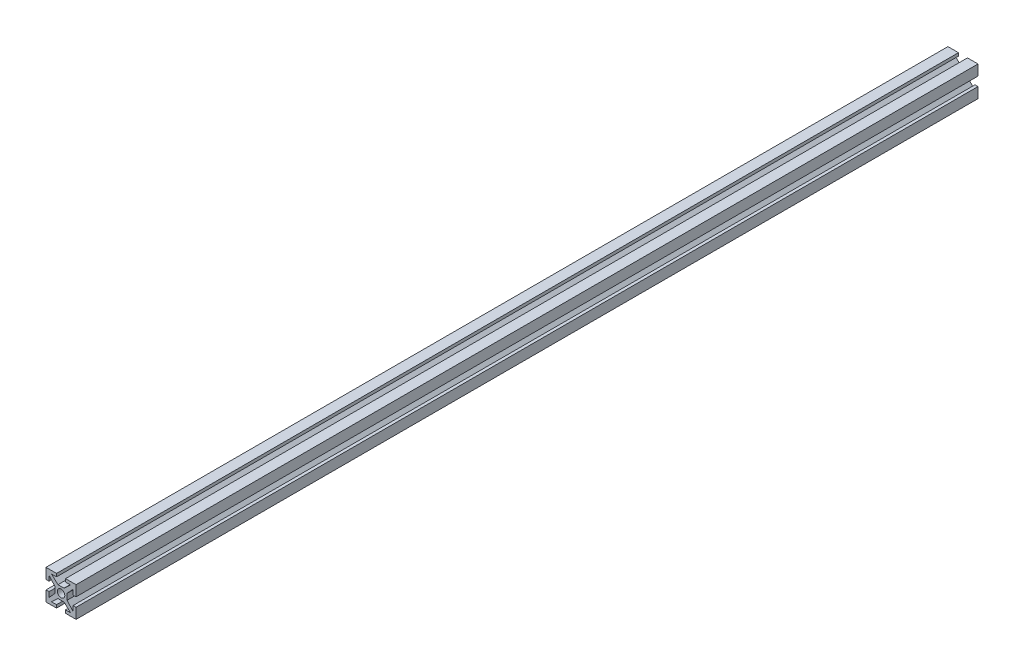
SolidWorks part; units mm, degrees
ref_plane "Front Plane" through (0, 0, 0) normal (0, 0, 1) x (1, 0, 0)
ref_plane "Top Plane" through (0, 0, 0) normal (0, 1, 0) x (1, 0, 0)
ref_plane "Right Plane" through (0, 0, 0) normal (1, 0, 0) x (0, 0, -1)
sketch "Sketch1" plane through (0, 0, 0) normal (0, 0, 1) x (1, 0, 0)
  line L0 (-4.0492, 2) -> (2, 2) construction
  line L1 (2, 2) -> (2, -4.2486) construction
  line L2 (0, 0) -> (0, 5) construction
  line L3 (0, 0) -> (6.7008, 0) construction
  line L4 (-4.0492, 5) -> (5, 5) construction
  line L5 (5, 5) -> (5, -5.8095) construction
  line L6 (1.5, 5) -> (5, 5)
  line L7 (5, 5) -> (5, 1.5)
  line L8 (5, 1.5) -> (4, 1.5)
  line L9 (4, 1.5) -> (4, 3.1816)
  line L10 (4, 3.1816) -> (2, 1)
  line L11 (2, 1) -> (2, 0)
  line L12 (1.5, 5) -> (1.5, 4)
  line L13 (1.5, 4) -> (3.1816, 4)
  line L14 (3.1816, 4) -> (1, 2)
  line L15 (1, 2) -> (0, 2)
  line L16 (0, 0) -> (7.554, 7.554) construction
  line L17 (5, -1.5) -> (5, -5)
  line L18 (5, -5) -> (1.5, -5)
  line L19 (1.5, -5) -> (1.5, -4)
  line L20 (1.5, -4) -> (3.1816, -4)
  line L21 (3.1816, -4) -> (1, -2)
  line L22 (1, -2) -> (0, -2)
  line L23 (5, -1.5) -> (4, -1.5)
  line L24 (4, -1.5) -> (4, -3.1816)
  line L25 (4, -3.1816) -> (2, -1)
  line L26 (2, -1) -> (2, 0)
  line L27 (0, 0) -> (5, 0) construction
  line L28 (-1.5, -5) -> (-5, -5)
  line L29 (-5, -5) -> (-5, -1.5)
  line L30 (-5, -1.5) -> (-4, -1.5)
  line L31 (-4, -1.5) -> (-4, -3.1816)
  line L32 (-4, -3.1816) -> (-2, -1)
  line L33 (-2, -1) -> (-2, 0)
  line L34 (-1.5, -5) -> (-1.5, -4)
  line L35 (-1.5, -4) -> (-3.1816, -4)
  line L36 (-3.1816, -4) -> (-1, -2)
  line L37 (-1, -2) -> (0, -2)
  line L38 (0, 0) -> (0, -5) construction
  line L39 (-5, 1.5) -> (-5, 5)
  line L40 (-5, 5) -> (-1.5, 5)
  line L41 (-1.5, 5) -> (-1.5, 4)
  line L42 (-1.5, 4) -> (-3.1816, 4)
  line L43 (-3.1816, 4) -> (-1, 2)
  line L44 (-1, 2) -> (0, 2)
  line L45 (-5, 1.5) -> (-4, 1.5)
  line L46 (-4, 1.5) -> (-4, 3.1816)
  line L47 (-4, 3.1816) -> (-2, 1)
  line L48 (-2, 1) -> (-2, 0)
  line L49 (0, 0) -> (-5, 0) construction
  circle A0 centre (0, 0) radius 1.25
  point P60 (0, 0)
  dimension "D10" = 4
  dimension "D11" = 2.5
  dimension "D1" = 2
  dimension "D2" = 2
  dimension "D3" = 5
  dimension "D4" = 5
  dimension "D5" = 1
  dimension "D6" = 1
  dimension "D7" = 3.5
  dimension "D8" = 3.5
  dimension "D9" = 1
extrude "Boss-Extrude2" add sketch "Sketch1" along normal blind 300 contours L47 L48 L33 L32 L31 L30 L29 L28 L34 L35 L36 L37 L22 L21 L20 L19 L18 L17 L23 L24 L25 L26 L11 L10 L9 L8 L7 L6 L12 L13 L14 L15 L44 L43 L42 L41 L40 L39 L45 L46 A0
